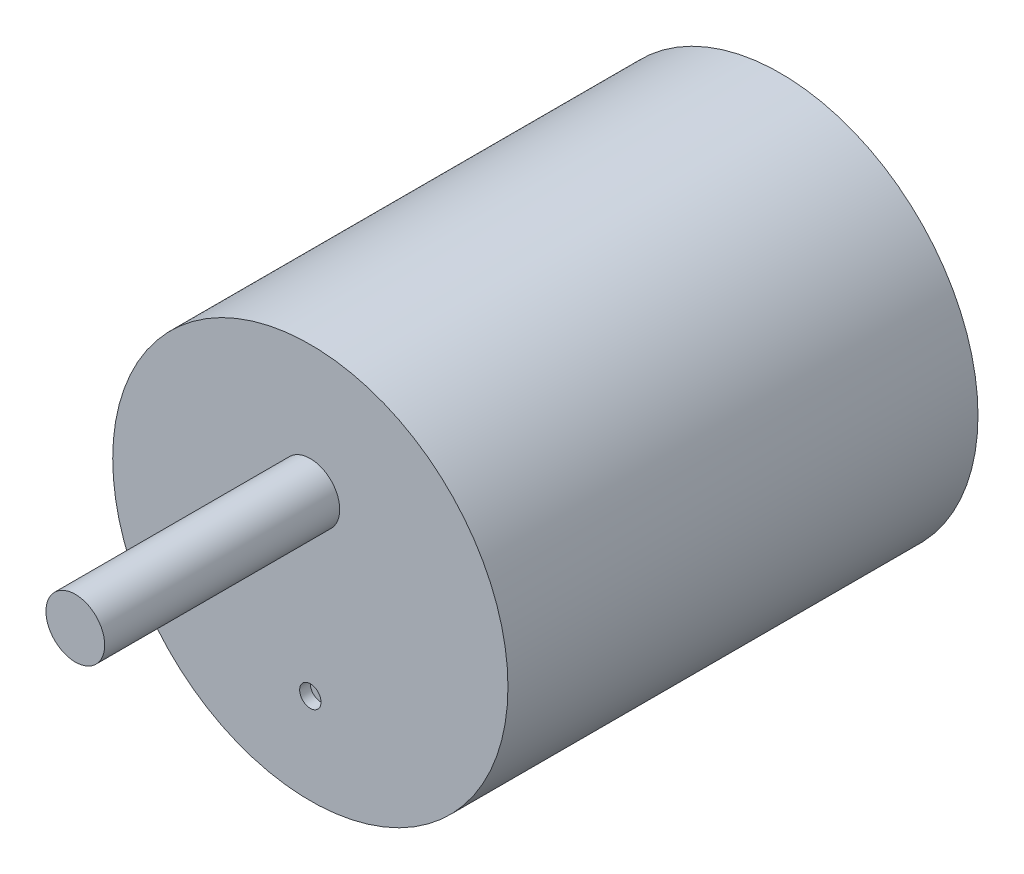
SolidWorks part; units mm, degrees
ref_plane "前视基准面" through (0, 0, 0) normal (0, 0, 1) x (1, 0, 0)
ref_plane "上视基准面" through (0, 0, 0) normal (0, 1, 0) x (1, 0, 0)
ref_plane "右视基准面" through (0, 0, 0) normal (1, 0, 0) x (0, 0, -1)
sketch "草图1" plane through (0, 0, 0) normal (0, 0, 1) x (1, 0, 0)
  circle A0 centre (0, 0) radius 18.5
  dimension "D1" = 37
extrude "凸台-拉伸1" add sketch "草图1" along normal blind 44
sketch "草图2" plane through (0, 0, 44) normal (0, 0, 1) x (1, 0, 0)
  line L0 (0, -18.5) -> (0, 18.5) construction
  circle A1 centre (0, 0) radius 18.5 construction
  circle A2 centre (0, 6.5) radius 2.75
  dimension "D1" = 25
  dimension "D2" = 5.5
extrude "凸台-拉伸2" add sketch "草图2" along normal blind 22
sketch "草图3" plane through (0, 0, 44) normal (0, 0, 1) x (1, 0, 0)
  line L0 (0, 6.5) -> (0, -10) construction
  circle A0 centre (0, -10) radius 1
  dimension "D1" = 10
extrude "切除-拉伸1" cut sketch "草图3" against normal blind 1
